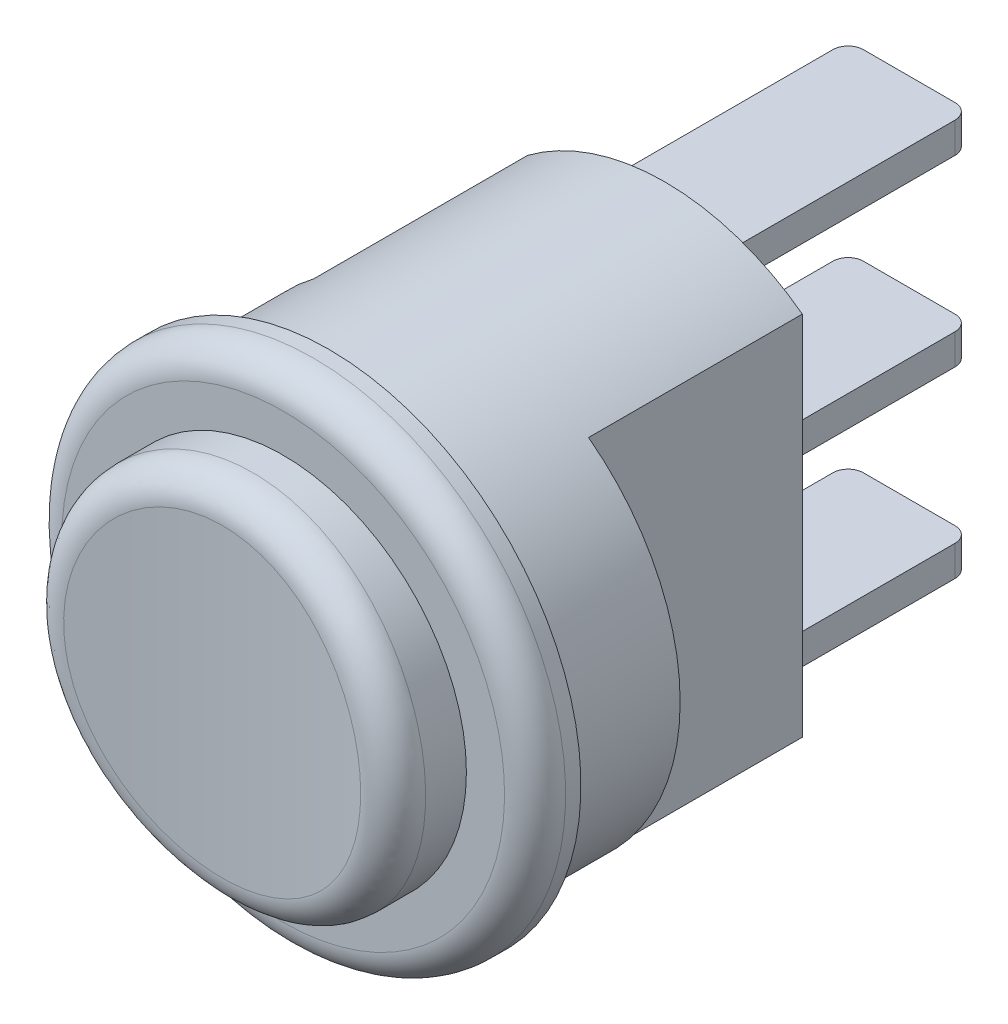
SolidWorks part; units mm, degrees
ref_plane "Спереди" through (0, 0, 0) normal (0, 0, 1) x (1, 0, 0)
ref_plane "Сверху" through (0, 0, 0) normal (0, 1, 0) x (1, 0, 0)
ref_plane "Справа" through (0, 0, 0) normal (1, 0, 0) x (0, 0, -1)
sketch "Эскиз1" plane through (0, 0, 0) normal (1, 0, 0) x (0, 0, -1)
  line L0 (0, 0) -> (0, 8.25)
  line L1 (0, 8.25) -> (1.5, 8.25)
  line L2 (1.5, 8.25) -> (1.5, 7.5)
  line L3 (1.5, 7.5) -> (12.5, 7.5)
  line L4 (12.5, 7.5) -> (12.5, 0)
  line L5 (12.5, 0) -> (0, 0)
  dimension "D1" = 8.25
  dimension "D2" = 1.5
  dimension "D3" = 7.5
  dimension "D4" = 12.5
revolve "Повернуть1" add sketch "Эскиз1" angle 360 about L5
sketch "Эскиз2" plane through (0, 0, -12.5) normal (0, 0, -1) x (-1, 0, 0)
  line L0 (-4.5, 0) -> (4.5, 0) construction
  line L1 (-4.5, -6) -> (-4.5, 6)
  line L2 (4.5, -6) -> (4.5, 6)
  arc A0 (4.5, -6) -> (4.5, 6) centre (0, 0) ccw
  circle A1 centre (0, 0) radius 7.5
  arc A2 (-4.5, 6) -> (-4.5, -6) centre (0, 0) ccw
  point P2 (0, 0)
  dimension "D1" = 9
  dimension "D2" = 0
extrude "Вырез-Вытянуть1" cut sketch "Эскиз2" against normal blind 7
sketch "Эскиз3" plane through (0, 0, 0) normal (0, 0, 1) x (1, 0, 0)
  circle A0 centre (0, 0) radius 6
  dimension "D1" = 12
extrude "Бобышка-Вытянуть1" add sketch "Эскиз3" along normal blind 2.5 separate body
sketch "Эскиз4" plane through (0, 0, 0) normal (0, 1, 0) x (1, 0, 0)
  line L0 (-6, -2.5) -> (6, -2.5)
  arc A0 (-6, -2.5) -> (6, -2.5) centre (0, -37.6135) cw
extrude "Вырез-Вытянуть2" cut sketch "Эскиз4" against normal mid plane 15
fillet "Скругление1" radius 1 1 edges at (5.8607, -1.2853, 2.4765)
fillet "Скругление2" radius 1 1 edges at (0, 8.25, 0)
sketch "Эскиз5" plane through (0, 0, -12.5) normal (0, 0, -1) x (-1, 0, 0)
  line L0 (2, 6.5) -> (-2, 6.5)
  line L1 (2, 0.5) -> (-2, 0.5)
  line L2 (2, 0.5) -> (2, -0.5)
  line L3 (2, -0.5) -> (-2, -0.5)
  line L4 (-2, 0.5) -> (-2, -0.5)
  line L5 (2, 0.5) -> (-2, -0.5) construction
  line L6 (2, -0.5) -> (-2, 0.5) construction
  line L7 (2, 6.5) -> (2, 5.5)
  line L8 (2, 5.5) -> (-2, 5.5)
  line L9 (-2, 6.5) -> (-2, 5.5)
  line L10 (2, 6.5) -> (-2, 5.5) construction
  line L11 (2, 5.5) -> (-2, 6.5) construction
  line L12 (2, -5.5) -> (-2, -5.5)
  line L13 (2, -5.5) -> (2, -6.5)
  line L14 (2, -6.5) -> (-2, -6.5)
  line L15 (-2, -5.5) -> (-2, -6.5)
  line L16 (2, -5.5) -> (-2, -6.5) construction
  line L17 (2, -6.5) -> (-2, -5.5) construction
  line L18 (0, 6) -> (0, 0) construction
  line L19 (0, 0) -> (0, -6) construction
  point P0 (0, 0)
  point P6 (0, 6)
  point P11 (0, -6)
  dimension "D1" = 1
  dimension "D2" = 4
  dimension "D3" = 1
  dimension "D4" = 4
  dimension "D5" = 1
  dimension "D6" = 4
  dimension "D7" = 6
  dimension "D8" = 6
extrude "Бобышка-Вытянуть2" add sketch "Эскиз5" along normal blind 8 separate body
fillet "Скругление3" radius 0.5 2 edges at (2, -6, -20.5) (-2, -6, -20.5)
fillet "Скругление4" radius 0.5 2 edges at (2, 0, -20.5) (-2, 0, -20.5)
fillet "Скругление5" radius 0.5 2 edges at (2, 6, -20.5) (-2, 6, -20.5)
equation "\"D8@Эскиз5\"=\"D7@Эскиз5\""
